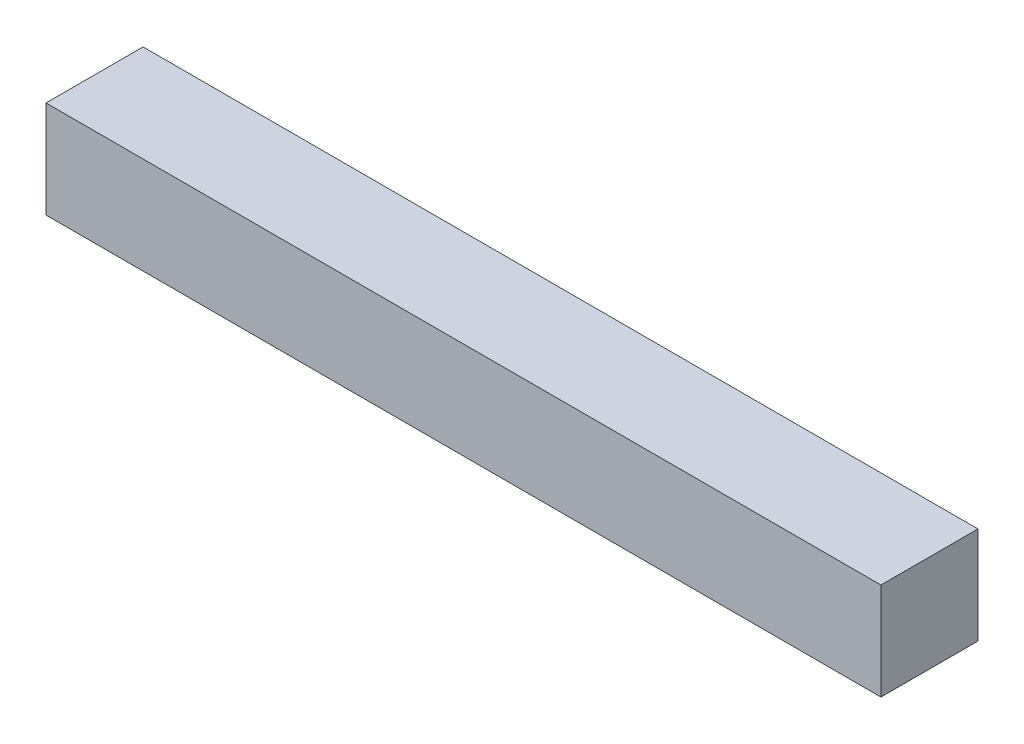
SolidWorks part; units mm, degrees
ref_plane "Front Plane" through (0, 0, 0) normal (0, 0, 1) x (1, 0, 0)
ref_plane "Top Plane" through (0, 0, 0) normal (0, 1, 0) x (1, 0, 0)
ref_plane "Right Plane" through (0, 0, 0) normal (1, 0, 0) x (0, 0, -1)
sketch "Sketch1" plane through (0, 0, 0) normal (1, 0, 0) x (0, 0, -1)
  line L1 (-5, -5) -> (5, -5)
  line L2 (-5, -5) -> (-5, 5)
  line L3 (-5, 5) -> (5, 5)
  line L4 (5, -5) -> (5, 5)
  line L5 (-5, -5) -> (5, 5) construction
  line L6 (-5, 5) -> (5, -5) construction
  point P0 (0, 0)
  dimension "D1" = 10
  dimension "D2" = 10
extrude "Boss-Extrude1" add sketch "Sketch1" along normal blind 86
